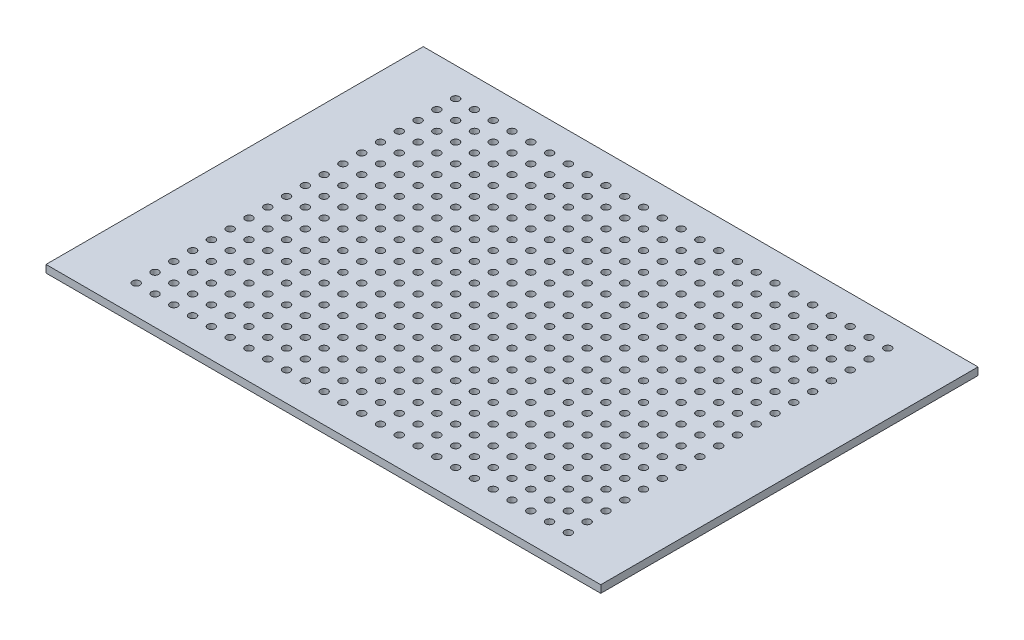
SolidWorks part; units mm, degrees
ref_plane "Front Plane" through (0, 0, 0) normal (0, 0, 1) x (1, 0, 0)
ref_plane "Top Plane" through (0, 0, 0) normal (0, 1, 0) x (1, 0, 0)
ref_plane "Right Plane" through (0, 0, 0) normal (1, 0, 0) x (0, 0, -1)
sketch "Sketch1" plane through (0, 0, 0) normal (0, 1, 0) x (1, 0, 0)
  line L1 (0, 0) -> (75, 0)
  line L2 (0, 0) -> (0, 51)
  line L3 (0, 51) -> (75, 51)
  line L4 (75, 0) -> (75, 51)
  circle A0 centre (8.29, 3.91) radius 0.5
  circle A1 centre (10.83, 3.91) radius 0.5
  circle A2 centre (13.37, 3.91) radius 0.5
  circle A3 centre (15.91, 3.91) radius 0.5
  circle A4 centre (18.45, 3.91) radius 0.5
  circle A5 centre (20.99, 3.91) radius 0.5
  circle A6 centre (23.53, 3.91) radius 0.5
  circle A7 centre (26.07, 3.91) radius 0.5
  circle A8 centre (28.61, 3.91) radius 0.5
  circle A9 centre (31.15, 3.91) radius 0.5
  circle A10 centre (33.69, 3.91) radius 0.5
  circle A11 centre (36.23, 3.91) radius 0.5
  circle A12 centre (38.77, 3.91) radius 0.5
  circle A13 centre (41.31, 3.91) radius 0.5
  circle A14 centre (43.85, 3.91) radius 0.5
  circle A15 centre (46.39, 3.91) radius 0.5
  circle A16 centre (48.93, 3.91) radius 0.5
  circle A17 centre (51.47, 3.91) radius 0.5
  circle A18 centre (54.01, 3.91) radius 0.5
  circle A19 centre (56.55, 3.91) radius 0.5
  circle A20 centre (59.09, 3.91) radius 0.5
  circle A21 centre (61.63, 3.91) radius 0.5
  circle A22 centre (64.17, 3.91) radius 0.5
  circle A23 centre (66.71, 3.91) radius 0.5
  circle A24 centre (10.83, 6.45) radius 0.5
  circle A25 centre (13.37, 6.45) radius 0.5
  circle A26 centre (15.91, 6.45) radius 0.5
  circle A27 centre (18.45, 6.45) radius 0.5
  circle A28 centre (20.99, 6.45) radius 0.5
  circle A29 centre (23.53, 6.45) radius 0.5
  circle A30 centre (26.07, 6.45) radius 0.5
  circle A31 centre (28.61, 6.45) radius 0.5
  circle A32 centre (31.15, 6.45) radius 0.5
  circle A33 centre (33.69, 6.45) radius 0.5
  circle A34 centre (36.23, 6.45) radius 0.5
  circle A35 centre (38.77, 6.45) radius 0.5
  circle A36 centre (41.31, 6.45) radius 0.5
  circle A37 centre (43.85, 6.45) radius 0.5
  circle A38 centre (46.39, 6.45) radius 0.5
  circle A39 centre (48.93, 6.45) radius 0.5
  circle A40 centre (51.47, 6.45) radius 0.5
  circle A41 centre (54.01, 6.45) radius 0.5
  circle A42 centre (56.55, 6.45) radius 0.5
  circle A43 centre (59.09, 6.45) radius 0.5
  circle A44 centre (61.63, 6.45) radius 0.5
  circle A45 centre (64.17, 6.45) radius 0.5
  circle A46 centre (66.71, 6.45) radius 0.5
  circle A47 centre (10.83, 8.99) radius 0.5
  circle A48 centre (13.37, 8.99) radius 0.5
  circle A49 centre (15.91, 8.99) radius 0.5
  circle A50 centre (18.45, 8.99) radius 0.5
  circle A51 centre (20.99, 8.99) radius 0.5
  circle A52 centre (23.53, 8.99) radius 0.5
  circle A53 centre (26.07, 8.99) radius 0.5
  circle A54 centre (28.61, 8.99) radius 0.5
  circle A55 centre (31.15, 8.99) radius 0.5
  circle A56 centre (33.69, 8.99) radius 0.5
  circle A57 centre (36.23, 8.99) radius 0.5
  circle A58 centre (38.77, 8.99) radius 0.5
  circle A59 centre (41.31, 8.99) radius 0.5
  circle A60 centre (43.85, 8.99) radius 0.5
  circle A61 centre (46.39, 8.99) radius 0.5
  circle A62 centre (48.93, 8.99) radius 0.5
  circle A63 centre (51.47, 8.99) radius 0.5
  circle A64 centre (54.01, 8.99) radius 0.5
  circle A65 centre (56.55, 8.99) radius 0.5
  circle A66 centre (59.09, 8.99) radius 0.5
  circle A67 centre (61.63, 8.99) radius 0.5
  circle A68 centre (64.17, 8.99) radius 0.5
  circle A69 centre (66.71, 8.99) radius 0.5
  circle A70 centre (10.83, 11.53) radius 0.5
  circle A71 centre (13.37, 11.53) radius 0.5
  circle A72 centre (15.91, 11.53) radius 0.5
  circle A73 centre (18.45, 11.53) radius 0.5
  circle A74 centre (20.99, 11.53) radius 0.5
  circle A75 centre (23.53, 11.53) radius 0.5
  circle A76 centre (26.07, 11.53) radius 0.5
  circle A77 centre (28.61, 11.53) radius 0.5
  circle A78 centre (31.15, 11.53) radius 0.5
  circle A79 centre (33.69, 11.53) radius 0.5
  circle A80 centre (36.23, 11.53) radius 0.5
  circle A81 centre (38.77, 11.53) radius 0.5
  circle A82 centre (41.31, 11.53) radius 0.5
  circle A83 centre (43.85, 11.53) radius 0.5
  circle A84 centre (46.39, 11.53) radius 0.5
  circle A85 centre (48.93, 11.53) radius 0.5
  circle A86 centre (51.47, 11.53) radius 0.5
  circle A87 centre (54.01, 11.53) radius 0.5
  circle A88 centre (56.55, 11.53) radius 0.5
  circle A89 centre (59.09, 11.53) radius 0.5
  circle A90 centre (61.63, 11.53) radius 0.5
  circle A91 centre (64.17, 11.53) radius 0.5
  circle A92 centre (66.71, 11.53) radius 0.5
  circle A93 centre (10.83, 14.07) radius 0.5
  circle A94 centre (13.37, 14.07) radius 0.5
  circle A95 centre (15.91, 14.07) radius 0.5
  circle A96 centre (18.45, 14.07) radius 0.5
  circle A97 centre (20.99, 14.07) radius 0.5
  circle A98 centre (23.53, 14.07) radius 0.5
  circle A99 centre (26.07, 14.07) radius 0.5
  circle A100 centre (28.61, 14.07) radius 0.5
  circle A101 centre (31.15, 14.07) radius 0.5
  circle A102 centre (33.69, 14.07) radius 0.5
  circle A103 centre (36.23, 14.07) radius 0.5
  circle A104 centre (38.77, 14.07) radius 0.5
  circle A105 centre (41.31, 14.07) radius 0.5
  circle A106 centre (43.85, 14.07) radius 0.5
  circle A107 centre (46.39, 14.07) radius 0.5
  circle A108 centre (48.93, 14.07) radius 0.5
  circle A109 centre (51.47, 14.07) radius 0.5
  circle A110 centre (54.01, 14.07) radius 0.5
  circle A111 centre (56.55, 14.07) radius 0.5
  circle A112 centre (59.09, 14.07) radius 0.5
  circle A113 centre (61.63, 14.07) radius 0.5
  circle A114 centre (64.17, 14.07) radius 0.5
  circle A115 centre (66.71, 14.07) radius 0.5
  circle A116 centre (10.83, 16.61) radius 0.5
  circle A117 centre (13.37, 16.61) radius 0.5
  circle A118 centre (15.91, 16.61) radius 0.5
  circle A119 centre (18.45, 16.61) radius 0.5
  circle A120 centre (20.99, 16.61) radius 0.5
  circle A121 centre (23.53, 16.61) radius 0.5
  circle A122 centre (26.07, 16.61) radius 0.5
  circle A123 centre (28.61, 16.61) radius 0.5
  circle A124 centre (31.15, 16.61) radius 0.5
  circle A125 centre (33.69, 16.61) radius 0.5
  circle A126 centre (36.23, 16.61) radius 0.5
  circle A127 centre (38.77, 16.61) radius 0.5
  circle A128 centre (41.31, 16.61) radius 0.5
  circle A129 centre (43.85, 16.61) radius 0.5
  circle A130 centre (46.39, 16.61) radius 0.5
  circle A131 centre (48.93, 16.61) radius 0.5
  circle A132 centre (51.47, 16.61) radius 0.5
  circle A133 centre (54.01, 16.61) radius 0.5
  circle A134 centre (56.55, 16.61) radius 0.5
  circle A135 centre (59.09, 16.61) radius 0.5
  circle A136 centre (61.63, 16.61) radius 0.5
  circle A137 centre (64.17, 16.61) radius 0.5
  circle A138 centre (66.71, 16.61) radius 0.5
  circle A139 centre (10.83, 19.15) radius 0.5
  circle A140 centre (13.37, 19.15) radius 0.5
  circle A141 centre (15.91, 19.15) radius 0.5
  circle A142 centre (18.45, 19.15) radius 0.5
  circle A143 centre (20.99, 19.15) radius 0.5
  circle A144 centre (23.53, 19.15) radius 0.5
  circle A145 centre (26.07, 19.15) radius 0.5
  circle A146 centre (28.61, 19.15) radius 0.5
  circle A147 centre (31.15, 19.15) radius 0.5
  circle A148 centre (33.69, 19.15) radius 0.5
  circle A149 centre (36.23, 19.15) radius 0.5
  circle A150 centre (38.77, 19.15) radius 0.5
  circle A151 centre (41.31, 19.15) radius 0.5
  circle A152 centre (43.85, 19.15) radius 0.5
  circle A153 centre (46.39, 19.15) radius 0.5
  circle A154 centre (48.93, 19.15) radius 0.5
  circle A155 centre (51.47, 19.15) radius 0.5
  circle A156 centre (54.01, 19.15) radius 0.5
  circle A157 centre (56.55, 19.15) radius 0.5
  circle A158 centre (59.09, 19.15) radius 0.5
  circle A159 centre (61.63, 19.15) radius 0.5
  circle A160 centre (64.17, 19.15) radius 0.5
  circle A161 centre (66.71, 19.15) radius 0.5
  circle A162 centre (10.83, 21.69) radius 0.5
  circle A163 centre (13.37, 21.69) radius 0.5
  circle A164 centre (15.91, 21.69) radius 0.5
  circle A165 centre (18.45, 21.69) radius 0.5
  circle A166 centre (20.99, 21.69) radius 0.5
  circle A167 centre (23.53, 21.69) radius 0.5
  circle A168 centre (26.07, 21.69) radius 0.5
  circle A169 centre (28.61, 21.69) radius 0.5
  circle A170 centre (31.15, 21.69) radius 0.5
  circle A171 centre (33.69, 21.69) radius 0.5
  circle A172 centre (36.23, 21.69) radius 0.5
  circle A173 centre (38.77, 21.69) radius 0.5
  circle A174 centre (41.31, 21.69) radius 0.5
  circle A175 centre (43.85, 21.69) radius 0.5
  circle A176 centre (46.39, 21.69) radius 0.5
  circle A177 centre (48.93, 21.69) radius 0.5
  circle A178 centre (51.47, 21.69) radius 0.5
  circle A179 centre (54.01, 21.69) radius 0.5
  circle A180 centre (56.55, 21.69) radius 0.5
  circle A181 centre (59.09, 21.69) radius 0.5
  circle A182 centre (61.63, 21.69) radius 0.5
  circle A183 centre (64.17, 21.69) radius 0.5
  circle A184 centre (66.71, 21.69) radius 0.5
  circle A185 centre (10.83, 24.23) radius 0.5
  circle A186 centre (13.37, 24.23) radius 0.5
  circle A187 centre (15.91, 24.23) radius 0.5
  circle A188 centre (18.45, 24.23) radius 0.5
  circle A189 centre (20.99, 24.23) radius 0.5
  circle A190 centre (23.53, 24.23) radius 0.5
  circle A191 centre (26.07, 24.23) radius 0.5
  circle A192 centre (28.61, 24.23) radius 0.5
  circle A193 centre (31.15, 24.23) radius 0.5
  circle A194 centre (33.69, 24.23) radius 0.5
  circle A195 centre (36.23, 24.23) radius 0.5
  circle A196 centre (38.77, 24.23) radius 0.5
  circle A197 centre (41.31, 24.23) radius 0.5
  circle A198 centre (43.85, 24.23) radius 0.5
  circle A199 centre (46.39, 24.23) radius 0.5
  circle A200 centre (48.93, 24.23) radius 0.5
  circle A201 centre (51.47, 24.23) radius 0.5
  circle A202 centre (54.01, 24.23) radius 0.5
  circle A203 centre (56.55, 24.23) radius 0.5
  circle A204 centre (59.09, 24.23) radius 0.5
  circle A205 centre (61.63, 24.23) radius 0.5
  circle A206 centre (64.17, 24.23) radius 0.5
  circle A207 centre (66.71, 24.23) radius 0.5
  circle A208 centre (10.83, 26.77) radius 0.5
  circle A209 centre (13.37, 26.77) radius 0.5
  circle A210 centre (15.91, 26.77) radius 0.5
  circle A211 centre (18.45, 26.77) radius 0.5
  circle A212 centre (20.99, 26.77) radius 0.5
  circle A213 centre (23.53, 26.77) radius 0.5
  circle A214 centre (26.07, 26.77) radius 0.5
  circle A215 centre (28.61, 26.77) radius 0.5
  circle A216 centre (31.15, 26.77) radius 0.5
  circle A217 centre (33.69, 26.77) radius 0.5
  circle A218 centre (36.23, 26.77) radius 0.5
  circle A219 centre (38.77, 26.77) radius 0.5
  circle A220 centre (41.31, 26.77) radius 0.5
  circle A221 centre (43.85, 26.77) radius 0.5
  circle A222 centre (46.39, 26.77) radius 0.5
  circle A223 centre (48.93, 26.77) radius 0.5
  circle A224 centre (51.47, 26.77) radius 0.5
  circle A225 centre (54.01, 26.77) radius 0.5
  circle A226 centre (56.55, 26.77) radius 0.5
  circle A227 centre (59.09, 26.77) radius 0.5
  circle A228 centre (61.63, 26.77) radius 0.5
  circle A229 centre (64.17, 26.77) radius 0.5
  circle A230 centre (66.71, 26.77) radius 0.5
  circle A231 centre (10.83, 29.31) radius 0.5
  circle A232 centre (13.37, 29.31) radius 0.5
  circle A233 centre (15.91, 29.31) radius 0.5
  circle A234 centre (18.45, 29.31) radius 0.5
  circle A235 centre (20.99, 29.31) radius 0.5
  circle A236 centre (23.53, 29.31) radius 0.5
  circle A237 centre (26.07, 29.31) radius 0.5
  circle A238 centre (28.61, 29.31) radius 0.5
  circle A239 centre (31.15, 29.31) radius 0.5
  circle A240 centre (33.69, 29.31) radius 0.5
  circle A241 centre (36.23, 29.31) radius 0.5
  circle A242 centre (38.77, 29.31) radius 0.5
  circle A243 centre (41.31, 29.31) radius 0.5
  circle A244 centre (43.85, 29.31) radius 0.5
  circle A245 centre (46.39, 29.31) radius 0.5
  circle A246 centre (48.93, 29.31) radius 0.5
  circle A247 centre (51.47, 29.31) radius 0.5
  circle A248 centre (54.01, 29.31) radius 0.5
  circle A249 centre (56.55, 29.31) radius 0.5
  circle A250 centre (59.09, 29.31) radius 0.5
  circle A251 centre (61.63, 29.31) radius 0.5
  circle A252 centre (64.17, 29.31) radius 0.5
  circle A253 centre (66.71, 29.31) radius 0.5
  circle A254 centre (10.83, 31.85) radius 0.5
  circle A255 centre (13.37, 31.85) radius 0.5
  circle A256 centre (15.91, 31.85) radius 0.5
  circle A257 centre (18.45, 31.85) radius 0.5
  circle A258 centre (20.99, 31.85) radius 0.5
  circle A259 centre (23.53, 31.85) radius 0.5
  circle A260 centre (26.07, 31.85) radius 0.5
  circle A261 centre (28.61, 31.85) radius 0.5
  circle A262 centre (31.15, 31.85) radius 0.5
  circle A263 centre (33.69, 31.85) radius 0.5
  circle A264 centre (36.23, 31.85) radius 0.5
  circle A265 centre (38.77, 31.85) radius 0.5
  circle A266 centre (41.31, 31.85) radius 0.5
  circle A267 centre (43.85, 31.85) radius 0.5
  circle A268 centre (46.39, 31.85) radius 0.5
  circle A269 centre (48.93, 31.85) radius 0.5
  circle A270 centre (51.47, 31.85) radius 0.5
  circle A271 centre (54.01, 31.85) radius 0.5
  circle A272 centre (56.55, 31.85) radius 0.5
  circle A273 centre (59.09, 31.85) radius 0.5
  circle A274 centre (61.63, 31.85) radius 0.5
  circle A275 centre (64.17, 31.85) radius 0.5
  circle A276 centre (66.71, 31.85) radius 0.5
  circle A277 centre (10.83, 34.39) radius 0.5
  circle A278 centre (13.37, 34.39) radius 0.5
  circle A279 centre (15.91, 34.39) radius 0.5
  circle A280 centre (18.45, 34.39) radius 0.5
  circle A281 centre (20.99, 34.39) radius 0.5
  circle A282 centre (23.53, 34.39) radius 0.5
  circle A283 centre (26.07, 34.39) radius 0.5
  circle A284 centre (28.61, 34.39) radius 0.5
  circle A285 centre (31.15, 34.39) radius 0.5
  circle A286 centre (33.69, 34.39) radius 0.5
  circle A287 centre (36.23, 34.39) radius 0.5
  circle A288 centre (38.77, 34.39) radius 0.5
  circle A289 centre (41.31, 34.39) radius 0.5
  circle A290 centre (43.85, 34.39) radius 0.5
  circle A291 centre (46.39, 34.39) radius 0.5
  circle A292 centre (48.93, 34.39) radius 0.5
  circle A293 centre (51.47, 34.39) radius 0.5
  circle A294 centre (54.01, 34.39) radius 0.5
  circle A295 centre (56.55, 34.39) radius 0.5
  circle A296 centre (59.09, 34.39) radius 0.5
  circle A297 centre (61.63, 34.39) radius 0.5
  circle A298 centre (64.17, 34.39) radius 0.5
  circle A299 centre (66.71, 34.39) radius 0.5
  circle A300 centre (10.83, 36.93) radius 0.5
  circle A301 centre (13.37, 36.93) radius 0.5
  circle A302 centre (15.91, 36.93) radius 0.5
  circle A303 centre (18.45, 36.93) radius 0.5
  circle A304 centre (20.99, 36.93) radius 0.5
  circle A305 centre (23.53, 36.93) radius 0.5
  circle A306 centre (26.07, 36.93) radius 0.5
  circle A307 centre (28.61, 36.93) radius 0.5
  circle A308 centre (31.15, 36.93) radius 0.5
  circle A309 centre (33.69, 36.93) radius 0.5
  circle A310 centre (36.23, 36.93) radius 0.5
  circle A311 centre (38.77, 36.93) radius 0.5
  circle A312 centre (41.31, 36.93) radius 0.5
  circle A313 centre (43.85, 36.93) radius 0.5
  circle A314 centre (46.39, 36.93) radius 0.5
  circle A315 centre (48.93, 36.93) radius 0.5
  circle A316 centre (51.47, 36.93) radius 0.5
  circle A317 centre (54.01, 36.93) radius 0.5
  circle A318 centre (56.55, 36.93) radius 0.5
  circle A319 centre (59.09, 36.93) radius 0.5
  circle A320 centre (61.63, 36.93) radius 0.5
  circle A321 centre (64.17, 36.93) radius 0.5
  circle A322 centre (66.71, 36.93) radius 0.5
  circle A323 centre (10.83, 39.47) radius 0.5
  circle A324 centre (13.37, 39.47) radius 0.5
  circle A325 centre (15.91, 39.47) radius 0.5
  circle A326 centre (18.45, 39.47) radius 0.5
  circle A327 centre (20.99, 39.47) radius 0.5
  circle A328 centre (23.53, 39.47) radius 0.5
  circle A329 centre (26.07, 39.47) radius 0.5
  circle A330 centre (28.61, 39.47) radius 0.5
  circle A331 centre (31.15, 39.47) radius 0.5
  circle A332 centre (33.69, 39.47) radius 0.5
  circle A333 centre (36.23, 39.47) radius 0.5
  circle A334 centre (38.77, 39.47) radius 0.5
  circle A335 centre (41.31, 39.47) radius 0.5
  circle A336 centre (43.85, 39.47) radius 0.5
  circle A337 centre (46.39, 39.47) radius 0.5
  circle A338 centre (48.93, 39.47) radius 0.5
  circle A339 centre (51.47, 39.47) radius 0.5
  circle A340 centre (54.01, 39.47) radius 0.5
  circle A341 centre (56.55, 39.47) radius 0.5
  circle A342 centre (59.09, 39.47) radius 0.5
  circle A343 centre (61.63, 39.47) radius 0.5
  circle A344 centre (64.17, 39.47) radius 0.5
  circle A345 centre (66.71, 39.47) radius 0.5
  circle A346 centre (10.83, 42.01) radius 0.5
  circle A347 centre (13.37, 42.01) radius 0.5
  circle A348 centre (15.91, 42.01) radius 0.5
  circle A349 centre (18.45, 42.01) radius 0.5
  circle A350 centre (20.99, 42.01) radius 0.5
  circle A351 centre (23.53, 42.01) radius 0.5
  circle A352 centre (26.07, 42.01) radius 0.5
  circle A353 centre (28.61, 42.01) radius 0.5
  circle A354 centre (31.15, 42.01) radius 0.5
  circle A355 centre (33.69, 42.01) radius 0.5
  circle A356 centre (36.23, 42.01) radius 0.5
  circle A357 centre (38.77, 42.01) radius 0.5
  circle A358 centre (41.31, 42.01) radius 0.5
  circle A359 centre (43.85, 42.01) radius 0.5
  circle A360 centre (46.39, 42.01) radius 0.5
  circle A361 centre (48.93, 42.01) radius 0.5
  circle A362 centre (51.47, 42.01) radius 0.5
  circle A363 centre (54.01, 42.01) radius 0.5
  circle A364 centre (56.55, 42.01) radius 0.5
  circle A365 centre (59.09, 42.01) radius 0.5
  circle A366 centre (61.63, 42.01) radius 0.5
  circle A367 centre (64.17, 42.01) radius 0.5
  circle A368 centre (66.71, 42.01) radius 0.5
  circle A369 centre (10.83, 44.55) radius 0.5
  circle A370 centre (13.37, 44.55) radius 0.5
  circle A371 centre (15.91, 44.55) radius 0.5
  circle A372 centre (18.45, 44.55) radius 0.5
  circle A373 centre (20.99, 44.55) radius 0.5
  circle A374 centre (23.53, 44.55) radius 0.5
  circle A375 centre (26.07, 44.55) radius 0.5
  circle A376 centre (28.61, 44.55) radius 0.5
  circle A377 centre (31.15, 44.55) radius 0.5
  circle A378 centre (33.69, 44.55) radius 0.5
  circle A379 centre (36.23, 44.55) radius 0.5
  circle A380 centre (38.77, 44.55) radius 0.5
  circle A381 centre (41.31, 44.55) radius 0.5
  circle A382 centre (43.85, 44.55) radius 0.5
  circle A383 centre (46.39, 44.55) radius 0.5
  circle A384 centre (48.93, 44.55) radius 0.5
  circle A385 centre (51.47, 44.55) radius 0.5
  circle A386 centre (54.01, 44.55) radius 0.5
  circle A387 centre (56.55, 44.55) radius 0.5
  circle A388 centre (59.09, 44.55) radius 0.5
  circle A389 centre (61.63, 44.55) radius 0.5
  circle A390 centre (64.17, 44.55) radius 0.5
  circle A391 centre (66.71, 44.55) radius 0.5
  circle A392 centre (10.83, 47.09) radius 0.5
  circle A393 centre (13.37, 47.09) radius 0.5
  circle A394 centre (15.91, 47.09) radius 0.5
  circle A395 centre (18.45, 47.09) radius 0.5
  circle A396 centre (20.99, 47.09) radius 0.5
  circle A397 centre (23.53, 47.09) radius 0.5
  circle A398 centre (26.07, 47.09) radius 0.5
  circle A399 centre (28.61, 47.09) radius 0.5
  circle A400 centre (31.15, 47.09) radius 0.5
  circle A401 centre (33.69, 47.09) radius 0.5
  circle A402 centre (36.23, 47.09) radius 0.5
  circle A403 centre (38.77, 47.09) radius 0.5
  circle A404 centre (41.31, 47.09) radius 0.5
  circle A405 centre (43.85, 47.09) radius 0.5
  circle A406 centre (46.39, 47.09) radius 0.5
  circle A407 centre (48.93, 47.09) radius 0.5
  circle A408 centre (51.47, 47.09) radius 0.5
  circle A409 centre (54.01, 47.09) radius 0.5
  circle A410 centre (56.55, 47.09) radius 0.5
  circle A411 centre (59.09, 47.09) radius 0.5
  circle A412 centre (61.63, 47.09) radius 0.5
  circle A413 centre (64.17, 47.09) radius 0.5
  circle A414 centre (66.71, 47.09) radius 0.5
  circle A415 centre (8.29, 6.45) radius 0.5
  circle A416 centre (8.29, 8.99) radius 0.5
  circle A417 centre (8.29, 11.53) radius 0.5
  circle A418 centre (8.29, 14.07) radius 0.5
  circle A419 centre (8.29, 16.61) radius 0.5
  circle A420 centre (8.29, 19.15) radius 0.5
  circle A421 centre (8.29, 21.69) radius 0.5
  circle A422 centre (8.29, 24.23) radius 0.5
  circle A423 centre (8.29, 26.77) radius 0.5
  circle A424 centre (8.29, 29.31) radius 0.5
  circle A425 centre (8.29, 31.85) radius 0.5
  circle A426 centre (8.29, 34.39) radius 0.5
  circle A427 centre (8.29, 36.93) radius 0.5
  circle A428 centre (8.29, 39.47) radius 0.5
  circle A429 centre (8.29, 42.01) radius 0.5
  circle A430 centre (8.29, 44.55) radius 0.5
  circle A431 centre (8.29, 47.09) radius 0.5
  dimension "D3" = 1
  dimension "D1" = 51
  dimension "D2" = 75
  dimension "D6" = 8.29
  dimension "D7" = 3.91
  dimension "D4" = 24
  dimension "D5" = 18
extrude "Boss-Extrude1" add sketch "Sketch1" along normal blind 1.016
equation "\"D7@Sketch1\"=(\"D1@Sketch1\"-1.7)/2"
equation "\"D6@Sketch1\"=(\"D2@Sketch1\"-2.3)/2"
